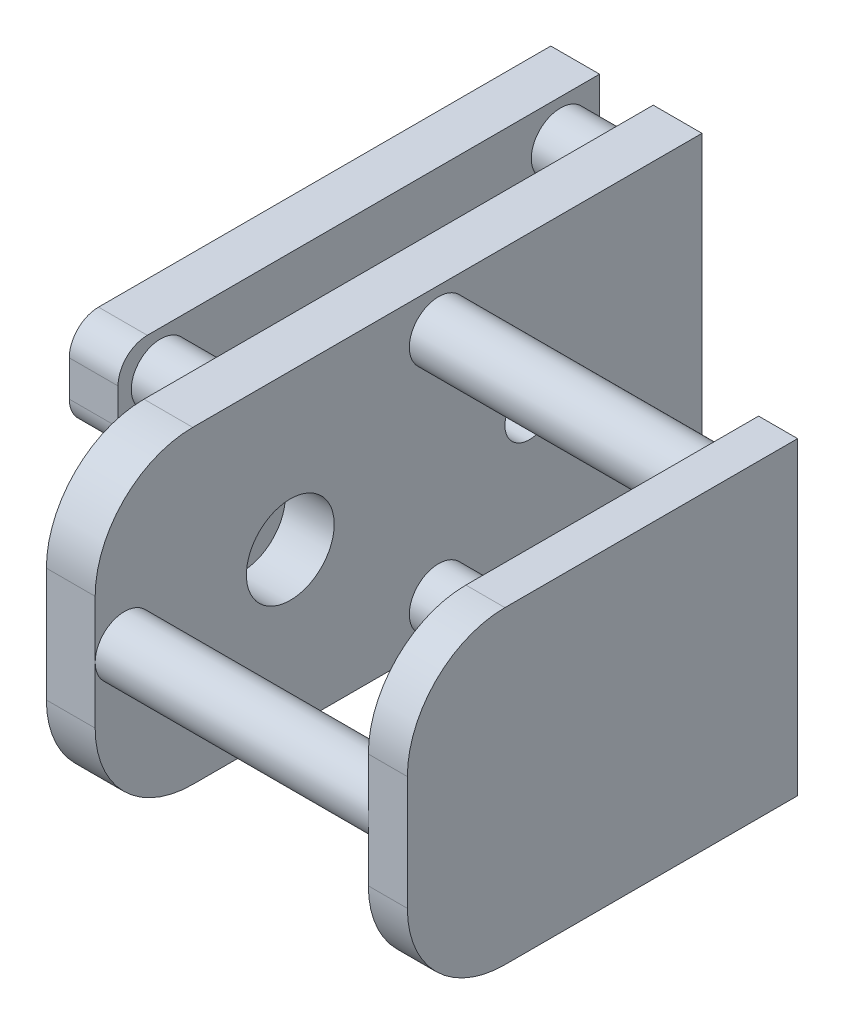
SolidWorks part; units mm, degrees
ref_plane "前视基准面" through (0, 0, 0) normal (0, 0, 1) x (1, 0, 0)
ref_plane "上视基准面" through (0, 0, 0) normal (0, 1, 0) x (1, 0, 0)
ref_plane "右视基准面" through (0, 0, 0) normal (1, 0, 0) x (0, 0, -1)
sketch "草图1" plane through (0, 0, 0) normal (1, 0, 0) x (0, 0, -1)
  line L1 (31.1, -15.85) -> (-21.1, -15.85)
  line L2 (31.1, -15.85) -> (31.1, 15.85)
  line L3 (31.1, 15.85) -> (-21.1, 15.85)
  line L4 (-31.1, -5.85) -> (-31.1, 5.85)
  line L5 (31.1, -15.85) -> (-31.1, 15.85) construction
  line L6 (31.1, 15.85) -> (-31.1, -15.85) construction
  circle A0 centre (-11.1, 0) radius 4.5
  circle A1 centre (13.4, 0) radius 2.5
  arc A2 (-31.1, -5.85) -> (-21.1, -15.85) centre (-21.1, -5.85) ccw
  arc A3 (-21.1, 15.85) -> (-31.1, 5.85) centre (-21.1, 5.85) ccw
  point P0 (0, 0)
  dimension "D3" = 9
  dimension "D6" = 5
  dimension "D7" = 10
  dimension "D1" = 31.7
  dimension "D2" = 62.2
  dimension "D4" = 20
  dimension "D5" = 17.7
extrude "凸台-拉伸1" add sketch "草图1" along normal blind 5
sketch "草图2" plane through (5, 0, 0) normal (1, 0, 0) x (0, 0, -1)
  line L0 (-31.1, 5.85) -> (-31.1, -5.85) construction
  line L1 (31.1, 15.85) -> (-21.1, 15.85) construction
  line L2 (-21.1, -15.85) -> (31.1, -15.85) construction
  line L3 (31.1, -15.85) -> (31.1, 15.85) construction
  circle A0 centre (-28.1, 0) radius 3
  circle A1 centre (4.1, 11.85) radius 3
  circle A2 centre (4.1, -11.85) radius 3
  dimension "D1" = 6
  dimension "D2" = 6
  dimension "D3" = 6
  dimension "D4" = 3
  dimension "D5" = 4
  dimension "D6" = 4
  dimension "D7" = 27
  dimension "D8" = 27
extrude "凸台-拉伸2" add sketch "草图2" along normal blind 28
sketch "草图3" plane through (33, 0, 0) normal (1, 0, 0) x (0, 0, -1)
  line L0 (31.1, 15.85) -> (-21.1, 15.85) construction
  line L1 (-21.1, -15.85) -> (31.1, -15.85) construction
  line L2 (-31.1, 0) -> (-31.1, -5.85) construction
  line L3 (-31.1, 5.85) -> (-31.1, 0) construction
  line L4 (8.9, 15.85) -> (-21.1, 15.85)
  line L5 (-21.1, -15.85) -> (8.9, -15.85)
  line L6 (-31.1, 0) -> (-31.1, -5.85)
  line L7 (-31.1, 5.85) -> (-31.1, 0)
  line L8 (8.9, 15.85) -> (8.9, -15.85)
  arc A0 (-31.1, -5.85) -> (-21.1, -15.85) centre (-21.1, -5.85) ccw construction
  arc A1 (-21.1, 15.85) -> (-31.1, 5.85) centre (-21.1, 5.85) ccw construction
  arc A2 (-31.1, -5.85) -> (-21.1, -15.85) centre (-21.1, -5.85) ccw
  arc A3 (-21.1, 15.85) -> (-31.1, 5.85) centre (-21.1, 5.85) ccw
  dimension "D1" = 40
extrude "凸台-拉伸3" add sketch "草图3" along normal blind 4
sketch "草图5" plane through (0, 0, 0) normal (-1, 0, 0) x (0, 0, 1)
  line L0 (-31.1, -15.85) -> (-31.1, 15.85) construction
  line L1 (-31.1, 15.85) -> (21.1, 15.85) construction
  circle A0 centre (-27.1, 11.85) radius 3
  circle A1 centre (-27.1, -11.9781) radius 3
  circle A2 centre (13.9, 11.85) radius 3
  circle A3 centre (13.9, -11.9781) radius 3
  dimension "D1" = 4
  dimension "D3" = 45
  dimension "D2" = 4
  dimension "D4" = 45
extrude "凸台-拉伸4" add sketch "草图5" along normal blind 5.5
sketch "草图6" plane through (-5.5, 0, 0) normal (-1, 0, 0) x (0, 0, 1)
  line L0 (21.1, -15.85) -> (-31.1, -15.85) construction
  line L1 (-31.1, -15.85) -> (-31.1, 15.85) construction
  line L2 (-31.1, 15.85) -> (21.1, 15.85) construction
  line L3 (15.2557, -15.85) -> (-31.1, -15.85)
  line L4 (-31.1, -15.85) -> (-31.1, 15.85)
  line L5 (-31.1, 15.85) -> (15.2557, 15.85)
  line L6 (18.2557, 12.85) -> (18.2557, 9.1837)
  line L7 (15.2557, 6.1837) -> (8.6961, 6.1837)
  line L8 (5.6961, 3.1837) -> (5.6961, -3.1837)
  line L9 (8.6961, -6.1837) -> (15.2557, -6.1837)
  line L10 (18.2557, -9.1837) -> (18.2557, -12.85)
  arc A0 (15.2557, -15.85) -> (18.2557, -12.85) centre (15.2557, -12.85) ccw
  arc A3 (18.2557, 12.85) -> (15.2557, 15.85) centre (15.2557, 12.85) ccw
  arc A4 (18.2557, -9.1837) -> (15.2557, -6.1837) centre (15.2557, -9.1837) ccw
  arc A5 (8.6961, -6.1837) -> (5.6961, -3.1837) centre (8.6961, -3.1837) cw
  arc A6 (8.6961, 6.1837) -> (5.6961, 3.1837) centre (8.6961, 3.1837) ccw
  arc A7 (18.2557, 9.1837) -> (15.2557, 6.1837) centre (15.2557, 9.1837) cw
  dimension "D2" = 3
extrude "凸台-拉伸6" add sketch "草图6" along normal blind 5
sketch "草图7" plane through (0, -15.85, 0) normal (0, -1, 0) x (1, 0, 0)
  line L3 (5, -31.1) -> (0, -31.1) construction
  circle A0 centre (2.5, 10.7) radius 1.6
  circle A1 centre (2.5, -23.1) radius 1.6
  dimension "D1" = 3.2
  dimension "D2" = 3.2
  dimension "D3" = 33.8
  dimension "D4" = 8
extrude "凸台-拉伸7" add sketch "草图7" along normal blind 1.4
